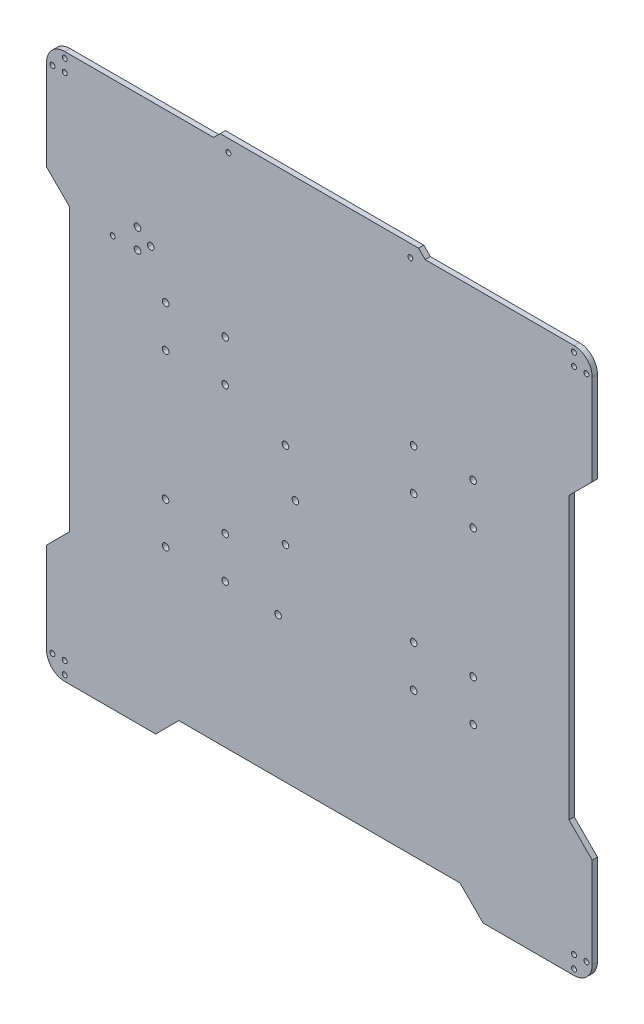
SolidWorks part; units mm, degrees
material "7050-T7651"
ref_plane "Front Plane" through (0, 0, 0) normal (0, 0, 1) x (1, 0, 0)
ref_plane "Top Plane" through (0, 0, 0) normal (0, 1, 0) x (1, 0, 0)
ref_plane "Right Plane" through (0, 0, 0) normal (1, 0, 0) x (0, 0, -1)
sketch "Sketch1" plane through (0, 0, 0) normal (0, 0, 1) x (1, 0, 0)
  line L0 (-154, 154) -> (154, -154) construction
  line L1 (-57, -39) -> (57, 39) construction
  line L2 (-93, 67.5) -> (-57, 67.5) construction
  line L3 (-93, 67.5) -> (-93, 39) construction
  line L4 (-93, 39) -> (-57, 39) construction
  line L5 (-57, 67.5) -> (-57, 39) construction
  line L6 (-93, -39) -> (-57, -39) construction
  line L7 (-93, -39) -> (-93, -67.5) construction
  line L8 (-93, -67.5) -> (-57, -67.5) construction
  line L9 (-57, -39) -> (-57, -67.5) construction
  line L10 (57, -39) -> (93, -39) construction
  line L11 (57, -39) -> (57, -67.5) construction
  line L12 (57, -67.5) -> (93, -67.5) construction
  line L13 (93, -39) -> (93, -67.5) construction
  line L14 (57, 67.5) -> (93, 67.5) construction
  line L15 (57, 67.5) -> (57, 39) construction
  line L16 (57, 39) -> (93, 39) construction
  line L17 (93, 67.5) -> (93, 39) construction
  line L18 (-75, 67.5) -> (-75, 39) construction
  line L19 (-75, -39) -> (-75, -67.5) construction
  line L20 (75, -39) -> (75, -67.5) construction
  line L21 (75, 39) -> (75, 67.5) construction
  line L22 (165, 154) -> (165, 99)
  line L23 (165, 99) -> (151, 85)
  line L24 (151, 85) -> (151, -85)
  line L25 (151, -85) -> (165, -99)
  line L26 (165, -99) -> (165, -154)
  line L27 (154, -165) -> (99, -165)
  line L28 (99, -165) -> (85, -151)
  line L29 (85, -151) -> (-85, -151)
  line L30 (-85, -151) -> (-99, -165)
  line L31 (-99, -165) -> (-154, -165)
  line L32 (-165, -154) -> (-165, -99)
  line L33 (-165, -99) -> (-151, -85)
  line L34 (-151, -85) -> (-151, 85)
  line L35 (-151, 85) -> (-165, 99)
  line L36 (-165, 99) -> (-165, 154)
  line L37 (-60, 169) -> (60, 169)
  line L38 (-55, 161.5) -> (55, 161.5) construction
  line L39 (0, 161.5) -> (0, 0) construction
  line L40 (60, 169) -> (64, 165)
  line L41 (64, 165) -> (154, 165)
  line L42 (-154, 165) -> (-64, 165)
  line L43 (-64, 165) -> (-60, 169)
  line L44 (-154, 161.5) -> (-154, 154) construction
  line L45 (154, 154) -> (161.5, 154) construction
  line L46 (-161.5, -154) -> (-154, -154) construction
  arc A0 (165, 154) -> (154, 165) centre (154, 154) ccw
  arc A1 (-154, 165) -> (-165, 154) centre (-154, 154) ccw
  arc A2 (165, -154) -> (154, -165) centre (154, -154) cw
  arc A3 (-154, -165) -> (-165, -154) centre (-154, -154) cw
  circle A4 centre (-14.5, -0.5) radius 2
  circle A5 centre (-93, 64) radius 2
  circle A6 centre (-93, 39) radius 2
  circle A7 centre (-57, 39) radius 2
  circle A8 centre (-57, 64) radius 2
  circle A9 centre (57, 39) radius 2
  circle A10 centre (57, 64) radius 2
  circle A11 centre (93, 39) radius 2
  circle A12 centre (93, 64) radius 2
  circle A13 centre (57, -64) radius 2
  circle A14 centre (57, -39) radius 2
  circle A15 centre (93, -39) radius 2
  circle A16 centre (93, -64) radius 2
  circle A17 centre (-93, -64) radius 2
  circle A18 centre (-57, -64) radius 2
  circle A19 centre (-57, -39) radius 2
  circle A20 centre (-93, -39) radius 2
  circle A21 centre (-20.5, -26.5) radius 2
  circle A22 centre (-161.5, 154) radius 1.5
  circle A23 centre (-154, 161.5) radius 1.5
  circle A24 centre (154, 161.5) radius 1.5
  circle A25 centre (161.5, 154) radius 1.5
  circle A26 centre (161.5, -154) radius 1.5
  circle A27 centre (0, 0) radius 2 construction
  circle A28 centre (-20.5, 25.5) radius 2
  circle A29 centre (-25, -65.5) radius 2
  circle A30 centre (154, -161.5) radius 1.5
  circle A31 centre (-161.5, -154) radius 1.5
  circle A32 centre (-154, -161.5) radius 1.5
  circle A33 centre (-110, 95) radius 2
  circle A34 centre (-110, 83) radius 2
  circle A35 centre (-102, 89) radius 2
  circle A36 centre (-125, 83) radius 1.5
  circle A39 centre (-154, 154) radius 1.5
  circle A40 centre (154, 154) radius 1.5
  circle A41 centre (154, -154) radius 1.5
  circle A42 centre (-154, -154) radius 1.5
  circle A43 centre (-55, 161.5) radius 1.5
  circle A44 centre (55, 161.5) radius 1.5
  point P2 (165, 169)
  point P97 (7, -39.3827)
  dimension "D4" = 308
  dimension "D11" = 4
  dimension "D21" = 7.5
  dimension "D26" = 7.5
  dimension "D24" = 7.5
  dimension "D23" = 7.5
  dimension "D31" = 40
  dimension "D2" = 3
  dimension "D12" = 11
  dimension "D28" = 3
  dimension "D29" = 4
  dimension "D5" = 135
  dimension "D6" = 150
  dimension "D7" = 36
  dimension "D8" = 28.5
  dimension "D9" = 3.5
  dimension "D10" = 3.5
  dimension "D13" = 15
  dimension "D14" = 135
  dimension "D15" = 7.5
  dimension "D16" = 70
  dimension "D17" = 14
  dimension "D18" = 308
  dimension "D19" = 60
  dimension "D22" = 7.5
  dimension "D25" = 7.5
  dimension "D20" = 60
  dimension "D27" = 7.5
  dimension "D35" = 14
  dimension "D36" = 14
  dimension "D37" = 110
  dimension "D38" = 7.5
extrude "Boss-Extrude1" add sketch "Sketch1" along normal blind 3.175
